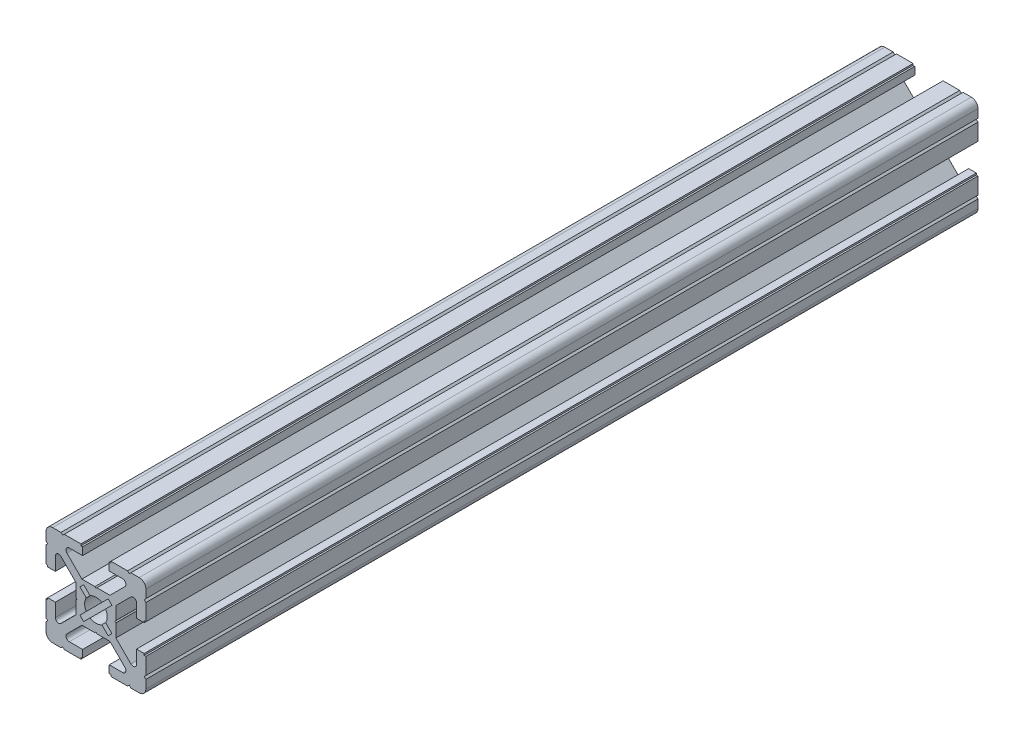
SolidWorks part; units mm, degrees
ref_plane "Front Plane" through (0, 0, 0) normal (0, 0, 1) x (1, 0, 0)
ref_plane "Top Plane" through (0, 0, 0) normal (0, 1, 0) x (1, 0, 0)
ref_plane "Right Plane" through (0, 0, 0) normal (1, 0, 0) x (0, 0, -1)
ref_plane "Plane1" through (0, 0, -150) normal (0, 0, -1) x (-1, 0, 0)
sketch "Sketch1" plane through (0, 0, -150) normal (0, 0, -1) x (-1, 0, 0)
  line L0 (4.8083, 3.677) -> (2.9023, 1.771)
  line L1 (2.9023, -1.771) -> (4.8083, -3.677)
  line L2 (4.8083, -3.677) -> (3.677, -4.8083)
  line L3 (3.677, -4.8083) -> (1.771, -2.9023)
  line L4 (-1.771, -2.9023) -> (-3.677, -4.8083)
  line L5 (-3.677, -4.8083) -> (-4.8083, -3.677)
  line L6 (-4.8083, -3.677) -> (-2.9023, -1.771)
  line L7 (-2.9023, 1.771) -> (-4.8083, 3.677)
  line L8 (-4.8083, 3.677) -> (-3.677, 4.8083)
  line L9 (-3.677, 4.8083) -> (-1.771, 2.9023)
  line L10 (1.771, 2.9023) -> (3.677, 4.8083)
  line L11 (3.677, 4.8083) -> (4.8083, 3.677)
  line L12 (-15, 13) -> (-15, 10.5)
  line L13 (-15, 10.5) -> (-14.5, 10)
  line L14 (-14.5, 10) -> (-15, 9.5)
  line L15 (-15, 9.5) -> (-15, 4.5)
  line L16 (-15, 4.5) -> (-14.5, 4.5)
  line L17 (-14.5, 4.5) -> (-14.5, 4)
  line L18 (-14.5, 4) -> (-12.2, 4)
  line L19 (-12.2, 4) -> (-12.2, 8)
  line L20 (-10.4929, 8.7071) -> (-6, 4.2142)
  line L21 (-6, 4.2142) -> (-6, 0.3125)
  line L22 (-6, 0.3125) -> (-5.7, 0)
  line L23 (-5.7, 0) -> (-6, -0.3125)
  line L24 (-6, -0.3125) -> (-6, -4.2142)
  line L25 (-6, -4.2142) -> (-10.4929, -8.7071)
  line L26 (-12.2, -8) -> (-12.2, -4)
  line L27 (-12.2, -4) -> (-14.5, -4)
  line L28 (-14.5, -4) -> (-14.5, -4.5)
  line L29 (-14.5, -4.5) -> (-15, -4.5)
  line L30 (-15, -4.5) -> (-15, -9.5)
  line L31 (-15, -9.5) -> (-14.5, -10)
  line L32 (-14.5, -10) -> (-15, -10.5)
  line L33 (-15, -10.5) -> (-15, -13)
  line L34 (-13, -15) -> (-10.5, -15)
  line L35 (-10.5, -15) -> (-10, -14.5)
  line L36 (-10, -14.5) -> (-9.5, -15)
  line L37 (-9.5, -15) -> (-4.5, -15)
  line L38 (-4.5, -15) -> (-4.5, -14.5)
  line L39 (-4.5, -14.5) -> (-4, -14.5)
  line L40 (-4, -14.5) -> (-4, -12.2)
  line L41 (-4, -12.2) -> (-8, -12.2)
  line L42 (-8.7071, -10.4929) -> (-4.2142, -6)
  line L43 (-4.2142, -6) -> (-0.3125, -6)
  line L44 (-0.3125, -6) -> (0, -5.7)
  line L45 (0, -5.7) -> (0.3125, -6)
  line L46 (0.3125, -6) -> (4.2142, -6)
  line L47 (4.2142, -6) -> (8.7071, -10.4929)
  line L48 (8, -12.2) -> (4, -12.2)
  line L49 (4, -12.2) -> (4, -14.5)
  line L50 (4, -14.5) -> (4.5, -14.5)
  line L51 (4.5, -14.5) -> (4.5, -15)
  line L52 (4.5, -15) -> (9.5, -15)
  line L53 (9.5, -15) -> (9.9899, -14.5)
  line L54 (9.9899, -14.5) -> (10.4899, -15)
  line L55 (10.4899, -15) -> (13, -15)
  line L56 (15, -13) -> (15, -10.5)
  line L57 (15, -10.5) -> (14.5, -10)
  line L58 (14.5, -10) -> (15, -9.5)
  line L59 (15, -9.5) -> (15, -4.5)
  line L60 (15, -4.5) -> (14.5, -4.5)
  line L61 (14.5, -4.5) -> (14.5, -4)
  line L62 (14.5, -4) -> (12.2, -4)
  line L63 (12.2, -4) -> (12.2, -8)
  line L64 (10.4929, -8.7071) -> (6, -4.2142)
  line L65 (6, -4.2142) -> (6, -0.3125)
  line L66 (6, -0.3125) -> (5.7, 0)
  line L67 (5.7, 0) -> (6, 0.3125)
  line L68 (6, 0.3125) -> (6, 4.2142)
  line L69 (6, 4.2142) -> (10.4929, 8.7071)
  line L70 (12.2, 8) -> (12.2, 4)
  line L71 (12.2, 4) -> (14.5, 4)
  line L72 (14.5, 4) -> (14.5, 4.5)
  line L73 (14.5, 4.5) -> (15, 4.5)
  line L74 (15, 4.5) -> (15, 9.5)
  line L75 (15, 9.5) -> (14.5, 10)
  line L76 (14.5, 10) -> (15, 10.5)
  line L77 (15, 10.5) -> (15, 13)
  line L78 (13, 15) -> (10.5, 15)
  line L79 (10.5, 15) -> (10, 14.5)
  line L80 (10, 14.5) -> (9.5, 15)
  line L81 (9.5, 15) -> (4.5, 15)
  line L82 (4.5, 15) -> (4.5, 14.5)
  line L83 (4.5, 14.5) -> (4, 14.5)
  line L84 (4, 14.5) -> (4, 12.2)
  line L85 (4, 12.2) -> (8, 12.2)
  line L86 (8.7071, 10.4929) -> (4.2142, 6)
  line L87 (4.2142, 6) -> (0.3125, 6)
  line L88 (0.3125, 6) -> (0, 5.7)
  line L89 (0, 5.7) -> (-0.3125, 6)
  line L90 (-0.3125, 6) -> (-4.2142, 6)
  line L91 (-4.2142, 6) -> (-8.7071, 10.4929)
  line L92 (-8, 12.2) -> (-4, 12.2)
  line L93 (-4, 12.2) -> (-4, 14.5)
  line L94 (-4, 14.5) -> (-4.5, 14.5)
  line L95 (-4.5, 14.5) -> (-4.5, 15)
  line L96 (-4.5, 15) -> (-9.5, 15)
  line L97 (-9.5, 15) -> (-10, 14.5)
  line L98 (-10, 14.5) -> (-10.5, 15)
  line L99 (-10.5, 15) -> (-13, 15)
  arc A0 (2.9023, 1.771) -> (2.9023, -1.771) centre (0, 0) cw
  arc A1 (1.771, -2.9023) -> (-1.771, -2.9023) centre (0, 0) cw
  arc A2 (-2.9023, -1.771) -> (-2.9023, 1.771) centre (0, 0) cw
  arc A3 (-1.771, 2.9023) -> (1.771, 2.9023) centre (0, 0) cw
  arc A4 (-13, 15) -> (-15, 13) centre (-13, 13) ccw
  arc A5 (-12.2, 8) -> (-10.4929, 8.7071) centre (-11.2, 8) cw
  arc A6 (-10.4929, -8.7071) -> (-12.2, -8) centre (-11.2, -8) cw
  arc A7 (-15, -13) -> (-13, -15) centre (-13, -13) ccw
  arc A8 (-8, -12.2) -> (-8.7071, -10.4929) centre (-8, -11.2) cw
  arc A9 (8.7071, -10.4929) -> (8, -12.2) centre (8, -11.2) cw
  arc A10 (13, -15) -> (15, -13) centre (13, -13) ccw
  arc A11 (12.2, -8) -> (10.4929, -8.7071) centre (11.2, -8) cw
  arc A12 (10.4929, 8.7071) -> (12.2, 8) centre (11.2, 8) cw
  arc A13 (15, 13) -> (13, 15) centre (13, 13) ccw
  arc A14 (8, 12.2) -> (8.7071, 10.4929) centre (8, 11.2) cw
  arc A15 (-8.7071, 10.4929) -> (-8, 12.2) centre (-8, 11.2) cw
extrude "Boss-Extrude1" add sketch "Sketch1" against normal blind 250
ref_plane "Plane2" through (0, 0, -25) normal (0, 0, -1) x (-1, 0, 0)
